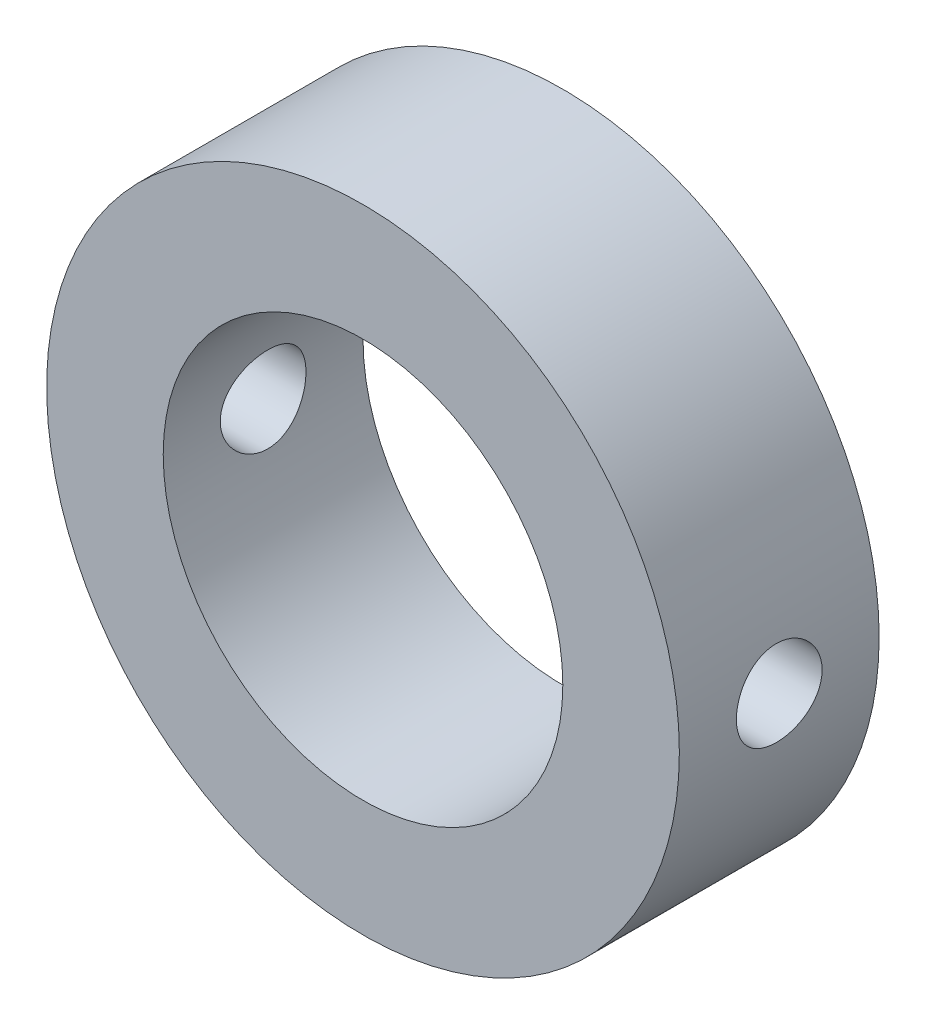
SolidWorks part; units mm, degrees
ref_plane "Front Plane" through (0, 0, 0) normal (0, 0, 1) x (1, 0, 0)
ref_plane "Top Plane" through (0, 0, 0) normal (0, 1, 0) x (1, 0, 0)
ref_plane "Right Plane" through (0, 0, 0) normal (1, 0, 0) x (0, 0, -1)
sketch "Sketch1" plane through (0, 0, 0) normal (0, 0, 1) x (1, 0, 0)
  circle A0 centre (0, 0) radius 19
  circle A1 centre (0, 0) radius 12
  dimension "D1" = 38
  dimension "D2" = 24
extrude "Boss-Extrude2" add sketch "Sketch1" along normal mid plane 12 contours A1 | A0
sketch "Sketch3" plane through (0, 0, 0) normal (1, 0, 0) x (0, 0, -1)
  circle A0 centre (0, 0) radius 2.5749
  dimension "D1" = 5.1497
extrude "Cut-Extrude1" cut sketch "Sketch3" against normal mid plane 72
